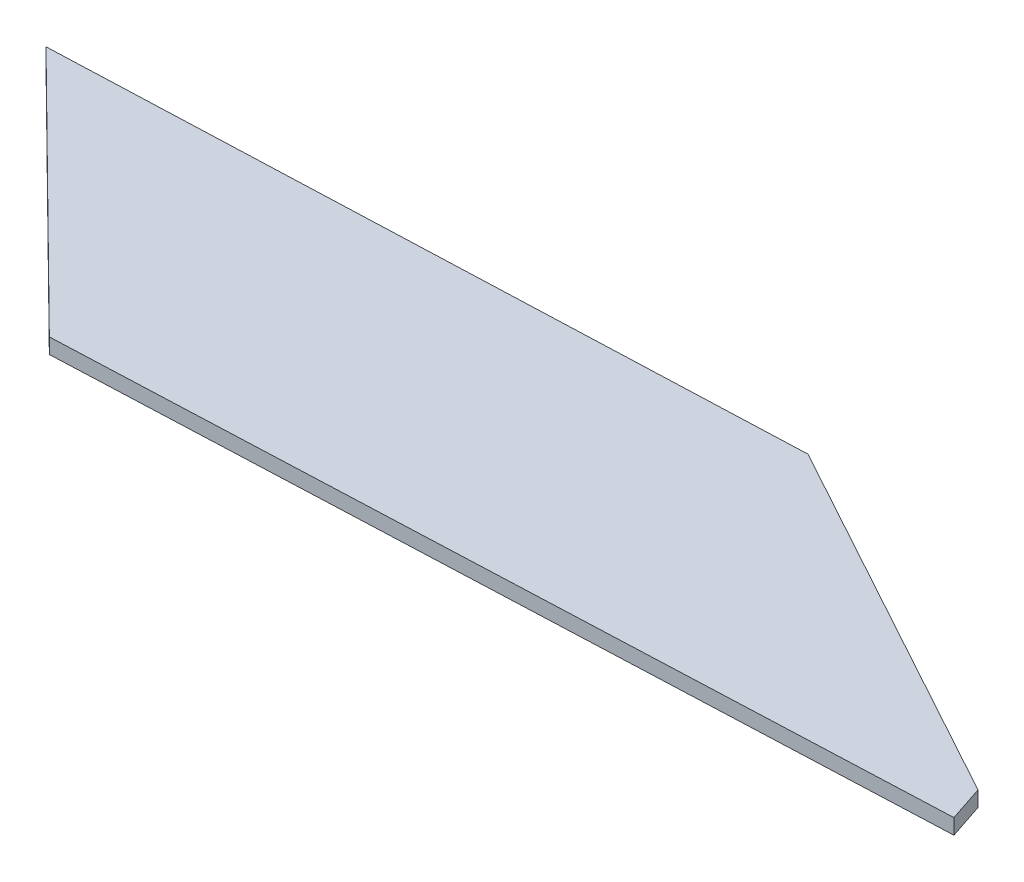
SolidWorks part; units mm, degrees
ref_plane "Plan de face" through (0, 0, 0) normal (0, 0, 1) x (1, 0, 0)
ref_plane "Plan de dessus" through (0, 0, 0) normal (0, 1, 0) x (1, 0, 0)
ref_plane "Plan de droite" through (0, 0, 0) normal (1, 0, 0) x (0, 0, -1)
sketch "Esquisse1" plane through (0, 0, 0) normal (0, 1, 0) x (1, 0, 0)
  line L0 (112.1755, 9.4319) -> (62.9646, 36.3788)
  line L1 (62.9646, 36.3788) -> (-33.1221, 32.6848)
  line L2 (-33.1221, 32.6848) -> (0, 0)
  line L3 (0, 0) -> (113.7384, 4.7175)
  line L4 (113.7384, 4.7175) -> (112.1755, 9.4319)
  point P5 (0, 0)
extrude "Boss.-Extru.1" add sketch "Esquisse1" along normal blind 2
